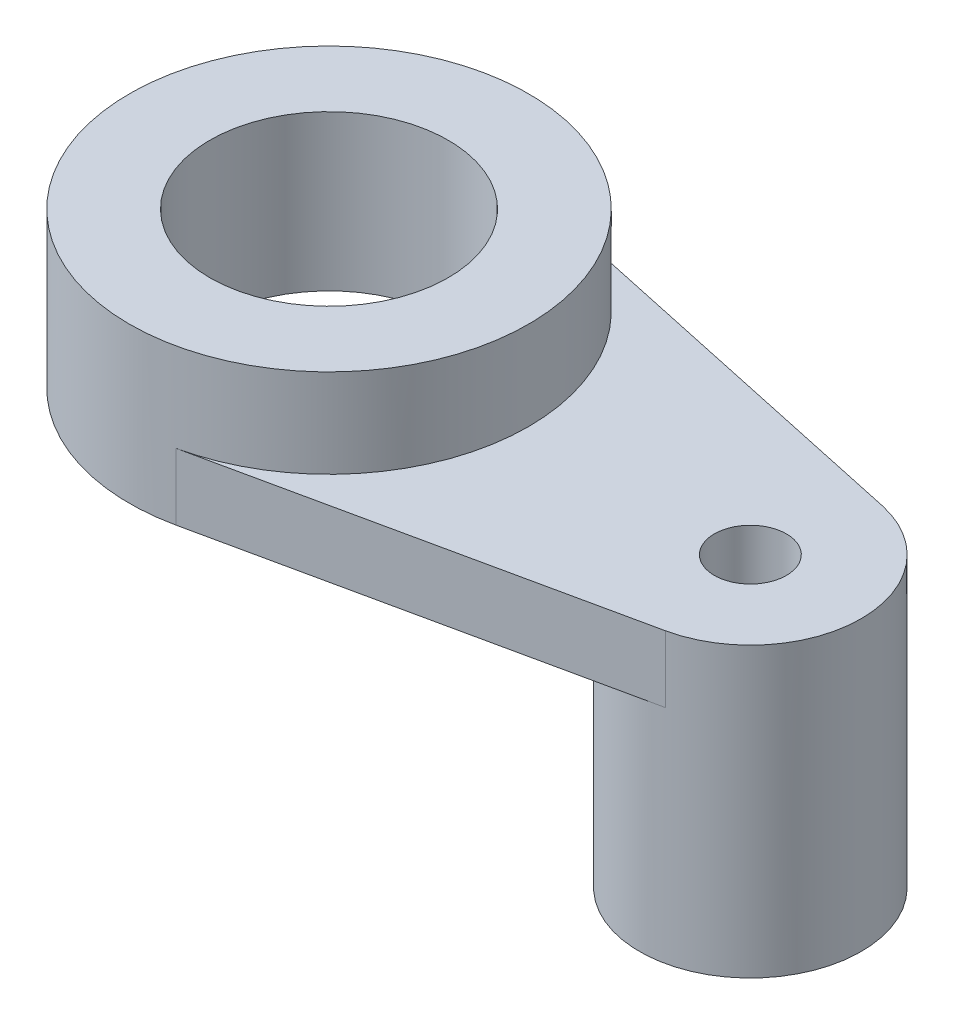
SolidWorks part; units mm, degrees
ref_plane "Front Plane" through (0, 0, 0) normal (0, 0, 1) x (1, 0, 0)
ref_plane "Top Plane" through (0, 0, 0) normal (0, 1, 0) x (1, 0, 0)
ref_plane "Right Plane" through (0, 0, 0) normal (1, 0, 0) x (0, 0, -1)
sketch "Sketch1" plane through (0, 0, 0) normal (0, 1, 0) x (1, 0, 0)
  circle A0 centre (0, 0) radius 18
  dimension "D1" = 36
extrude "Boss-Extrude1" add sketch "Sketch1" along normal blind 14
sketch "Sketch2" plane through (0, 0, 0) normal (0, -1, 0) x (1, 0, 0)
  line L0 (3.7895, 17.5966) -> (40.1053, 9.7759)
  line L1 (34.75, 0) -> (48, 0) construction
  line L2 (3.7895, -17.5966) -> (40.1053, -9.7759)
  circle A0 centre (38, 0) radius 3.25
  arc A1 (40.1053, -9.7759) -> (40.1053, 9.7759) centre (38, 0) ccw
  circle A3 centre (0, 0) radius 18 construction
  dimension "D2" = 6.5
  dimension "D3" = 20
  dimension "D1" = 38
extrude "Boss-Extrude2" add sketch "Sketch2" against normal blind 6
sketch "Sketch3" plane through (0, 0, 0) normal (0, -1, 0) x (1, 0, 0)
  circle A0 centre (38, 0) radius 10
  circle A1 centre (38, 0) radius 3.25
extrude "Boss-Extrude3" add sketch "Sketch3" along normal blind 20
sketch "Sketch4" plane through (0, 14, 0) normal (0, 1, 0) x (1, 0, 0)
  circle A0 centre (0, 0) radius 10.75
  dimension "D1" = 21.5
extrude "Cut-Extrude1" cut sketch "Sketch4" against normal up to next
